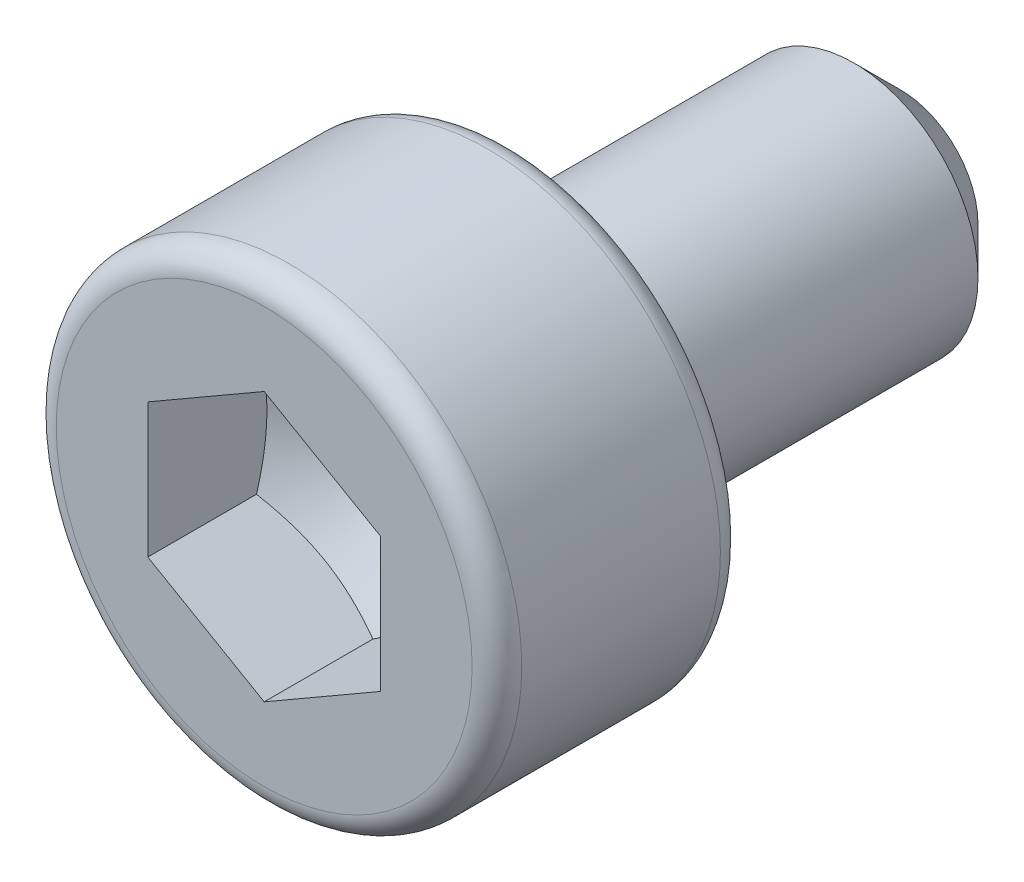
SolidWorks part; units mm, degrees
material "Alloy Steel"
ref_plane "Спереди" through (0, 0, 0) normal (0, 0, 1) x (1, 0, 0)
ref_plane "Сверху" through (0, 0, 0) normal (0, 1, 0) x (1, 0, 0)
ref_plane "Справа" through (0, 0, 0) normal (1, 0, 0) x (0, 0, -1)
sketch "Sketch1" plane through (0, 0, 0) normal (1, 0, 0) x (0, 0, -1)
  line L0 (0, 0) -> (4.1, 0) construction
  line L1 (0, 0) -> (0, 1.5)
  line L2 (0, 1.5) -> (1.6, 1.5)
  line L3 (1.6, 1.5) -> (1.6, 0.8)
  line L4 (1.6, 0.8) -> (4.1, 0.8)
  line L5 (4.1, 0.8) -> (4.1, 0)
  line L6 (0, 0) -> (4.1, 0)
  dimension "k" = 1.6
  dimension "Dk" = 3
  dimension "d" = 1.6
  dimension "L" = 2.5
revolve "RevolveBase" add sketch "Sketch1" angle 360 about L0
cosmetic thread "Cosmetic Thread1" parameters "D1"=2.5, "D2"=1.22
chamfer "ChamferRod" distance 0.3 angle 45 1 edges at (0.8, 0, -4.1)
fillet "FilletHead" radius 0.16 2 edges at (1.5, 0, -1.6) (1.5, 0, 0)
sketch "Sketch2" plane through (0, 0, 0) normal (0, 0, 1) x (1, 0, 0)
  line L1 (0, 0.866) -> (-0.75, 0.433)
  line L2 (-0.75, 0.433) -> (-0.75, -0.433)
  line L3 (-0.75, -0.433) -> (0, -0.866)
  line L4 (0, -0.866) -> (0.75, -0.433)
  line L5 (0.75, -0.433) -> (0.75, 0.433)
  line L6 (0.75, 0.433) -> (0, 0.866)
  circle A0 centre (0, 0) radius 0.75 construction
  circle A1 centre (0, 0) radius 0.8665 construction
  dimension "e" = 1.733
  dimension "S" = 1.5
extrude "HexHead" cut sketch "Sketch2" against normal blind 0.7
sketch "Sketch3" plane through (0, 0, -0.7) normal (0, 0, 1) x (1, 0, 0)
  line L1 (0, 0.866) -> (-0.75, 0.433)
  line L2 (-0.75, 0.433) -> (-0.75, -0.433)
  line L3 (-0.75, -0.433) -> (0, -0.866)
  line L4 (0, -0.866) -> (0.75, -0.433)
  line L5 (0.75, -0.433) -> (0.75, 0.433)
  line L6 (0.75, 0.433) -> (0, 0.866)
  circle A0 centre (0, 0) radius 0.75 construction
  dimension "D1" = 1.5
extrude "HexHead2" cut sketch "Sketch3" against normal blind 0.5546
sketch "Sketch4" plane through (0, 0, 0) normal (1, 0, 0) x (0, 0, -1)
  line L0 (0, 0) -> (4.1, 0) construction
  line L1 (4.1, -0.5) -> (4.1, 0.5) construction
  line L2 (1.2004, 0) -> (1.2546, 0)
  line L3 (1.2546, 0) -> (1.2546, 0.8668)
  line L4 (1.2546, 0.8668) -> (0.7, 0.8668)
  line L5 (0.7, 0.8668) -> (1.2004, 0)
  dimension "D1" = 1
  dimension "D2" = 1.5546
  dimension "D3" = 1.7335
  dimension "D4" = 60
revolve "RevolveHexHead" add sketch "Sketch4" angle 360 about L0
fillet "Fillet1" radius 0.1 1 edges at (0.8, 0, -1.6)
equation "\"D1@HexHead2\" = \"e@Sketch2\" * tan ( 60 ) "
equation "\"D1@Sketch3\"=\"S@Sketch2\""
equation "\"D1@Sketch4\"=\"t@HexHead\""
equation "\"D2@Sketch4\"=\"t@HexHead\"+\"D1@HexHead2\""
equation "\"D3@Sketch4\"=\"S@Sketch2\" * 1.1557"
